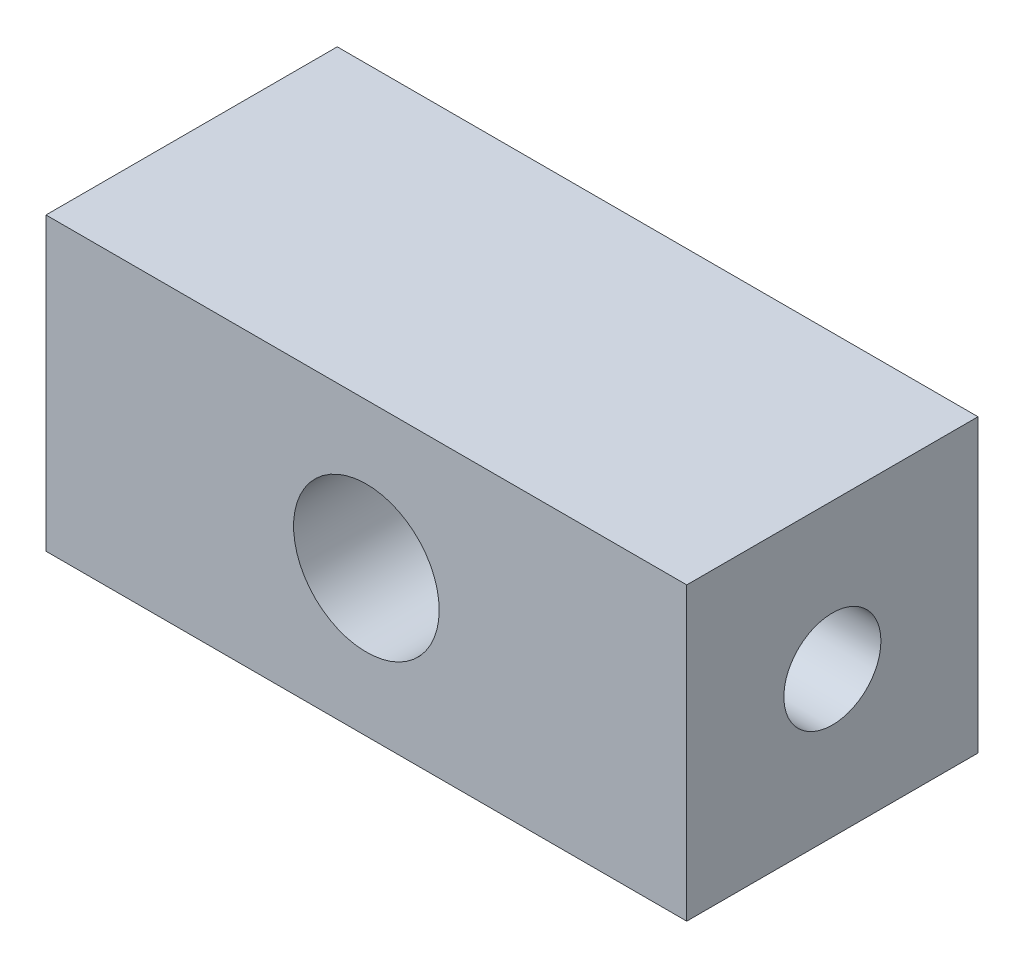
SolidWorks part; units mm, degrees
ref_plane "Alzado" through (0, 0, 0) normal (0, 0, 1) x (1, 0, 0)
ref_plane "Planta" through (0, 0, 0) normal (0, 1, 0) x (1, 0, 0)
ref_plane "Vista lateral" through (0, 0, 0) normal (1, 0, 0) x (0, 0, -1)
sketch "Croquis1" plane through (0, 0, 0) normal (0, 0, 1) x (1, 0, 0)
  line L1 (-33, -15) -> (33, -15)
  line L2 (-33, -15) -> (-33, 15)
  line L3 (-33, 15) -> (33, 15)
  line L4 (33, -15) -> (33, 15)
  line L5 (-33, -15) -> (33, 15) construction
  line L6 (-33, 15) -> (33, -15) construction
  circle A0 centre (0, 0) radius 7.5
  point P0 (0, 0)
  dimension "D3" = 15
  dimension "D1" = 30
  dimension "D2" = 66
extrude "Saliente-Extruir1" add sketch "Croquis1" along normal mid plane 30
sketch "Croquis2" plane through (33, 0, 0) normal (1, 0, 0) x (0, 0, -1)
  circle A0 centre (0, 0) radius 5
  dimension "D1" = 10
extrude "Cortar-Extruir1" cut sketch "Croquis2" against normal through all
